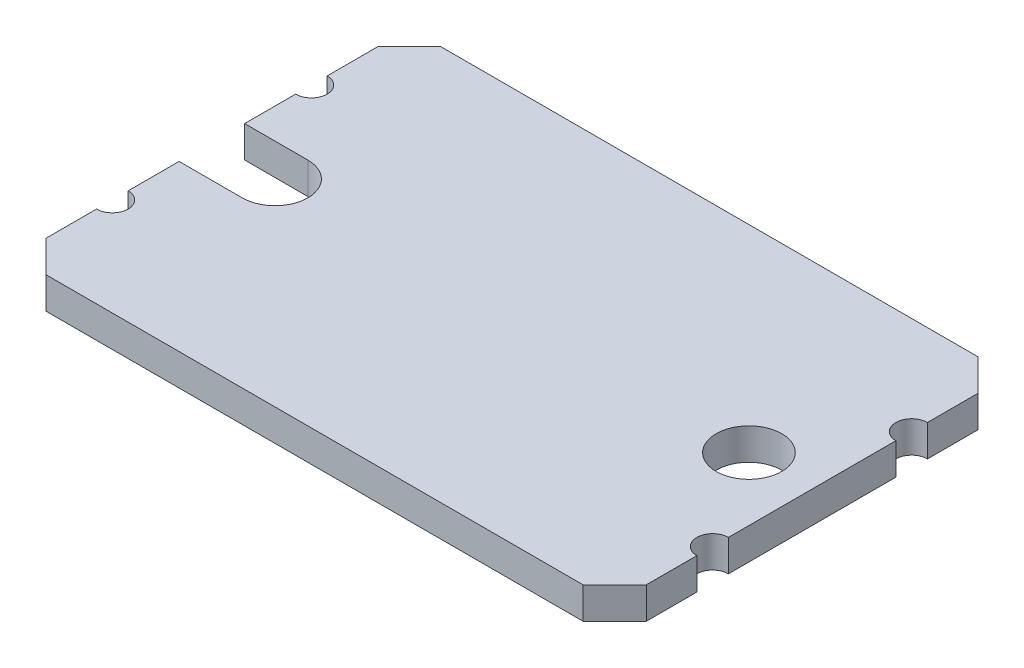
SolidWorks part; units mm, degrees
ref_plane "Front Plane" through (0, 0, 0) normal (0, 0, 1) x (1, 0, 0)
ref_plane "Top Plane" through (0, 0, 0) normal (0, 1, 0) x (1, 0, 0)
ref_plane "Right Plane" through (0, 0, 0) normal (1, 0, 0) x (0, 0, -1)
sketch "Sketch1" plane through (0, 0, 0) normal (0, 1, 0) x (1, 0, 0)
  line L0 (0, 12.5) -> (4, 12.5) construction
  line L1 (2, 0) -> (36, 0)
  line L5 (38, 12.5) -> (34, 12.5) construction
  line L6 (4, 14.575) -> (0, 14.575)
  line L7 (4, 10.425) -> (0, 10.425)
  line L8 (0, 12.5) -> (0, 18.8) construction
  line L9 (0, 12.5) -> (0, 6.2) construction
  line L10 (38, 12.5) -> (38, 6.2) construction
  line L11 (38, 12.5) -> (38, 18.8) construction
  line L12 (0, 0) -> (0, 2) construction
  line L13 (0, 0) -> (2, 0) construction
  line L14 (0, 25) -> (2, 25) construction
  line L15 (0, 25) -> (0, 23) construction
  line L16 (38, 25) -> (38, 23) construction
  line L17 (38, 0) -> (38, 2) construction
  line L18 (38, 0) -> (36, 0) construction
  line L19 (38, 25) -> (36, 25) construction
  line L20 (2, 0) -> (0, 2)
  line L21 (0, 2) -> (0, 5.2)
  line L22 (0, 7.2) -> (0, 10.425)
  line L23 (0, 14.575) -> (0, 17.8)
  line L24 (0, 19.8) -> (0, 23)
  line L25 (0, 23) -> (2, 25)
  line L26 (2, 25) -> (36, 25)
  line L27 (36, 25) -> (38, 23)
  line L28 (38, 23) -> (38, 19.8)
  line L29 (38, 17.8) -> (38, 7.2)
  line L30 (38, 5.2) -> (38, 2)
  line L31 (38, 2) -> (36, 0)
  arc A0 (4, 10.425) -> (4, 14.575) centre (4, 12.5) ccw
  circle A1 centre (34, 12.5) radius 2.075
  arc A2 (0, 7.2) -> (0, 5.2) centre (0, 6.2) cw
  arc A3 (0, 19.8) -> (0, 17.8) centre (0, 18.8) cw
  arc A4 (38, 17.8) -> (38, 19.8) centre (38, 18.8) cw
  arc A5 (38, 5.2) -> (38, 7.2) centre (38, 6.2) cw
extrude "Extrude1" add sketch "Sketch1" along normal blind 2
